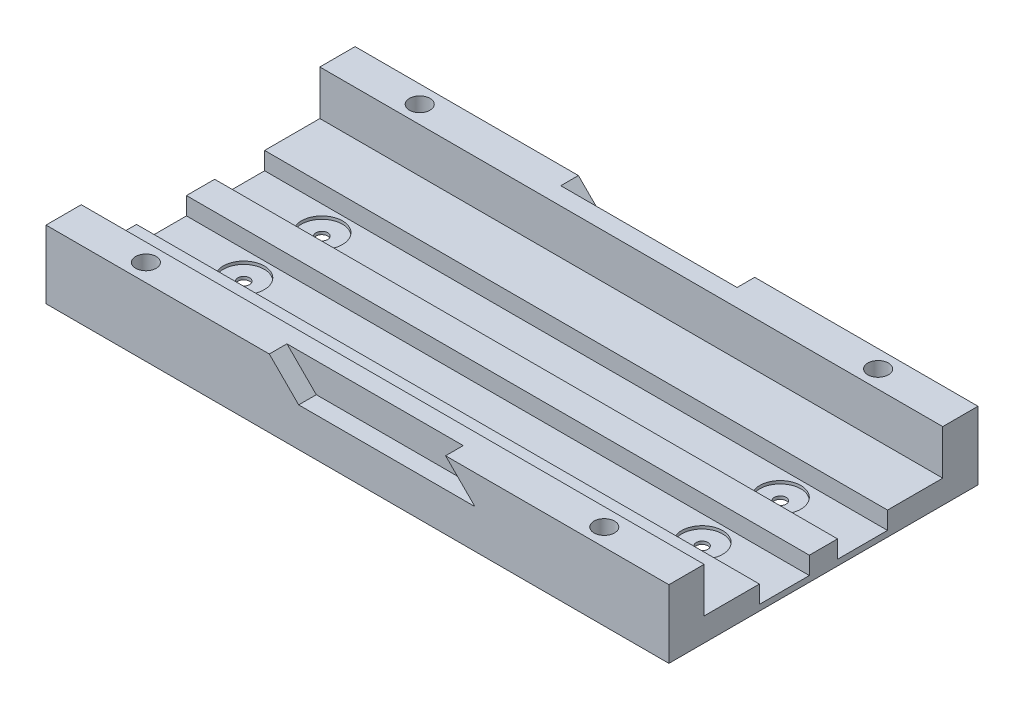
SolidWorks part; units mm, degrees
ref_plane "Front Plane" through (0, 0, 0) normal (0, 0, 1) x (1, 0, 0)
ref_plane "Top Plane" through (0, 0, 0) normal (0, 1, 0) x (1, 0, 0)
ref_plane "Right Plane" through (0, 0, 0) normal (1, 0, 0) x (0, 0, -1)
sketch "Sketch1" plane through (0, 0, 0) normal (0, 1, 0) x (1, 0, 0)
  line L1 (0, -13.3) -> (106, -13.3)
  line L2 (0, 0) -> (106, 0)
  line L3 (0, 0) -> (0, -4.8)
  line L4 (0, -4.8) -> (106, -4.8)
  line L5 (106, 0) -> (106, -4.8)
  line L6 (0, -13.3) -> (0, -4.8)
  line L7 (0, -4.8) -> (106, -4.8)
  line L8 (106, -13.3) -> (106, -4.8)
  line L9 (0, 0) -> (106, 0)
  line L10 (0, 0) -> (0, 8.5)
  line L11 (0, 8.5) -> (106, 8.5)
  line L12 (106, 0) -> (106, 8.5)
  line L13 (0, -22.7) -> (106, -22.7)
  line L14 (0, -22.7) -> (0, -13.3)
  line L15 (0, -13.3) -> (106, -13.3)
  line L16 (106, -22.7) -> (106, -13.3)
  line L17 (106, 8.5) -> (0, 8.5)
  line L18 (106, 8.5) -> (106, 17.9)
  line L19 (106, 17.9) -> (0, 17.9)
  line L20 (0, 8.5) -> (0, 17.9)
  line L21 (106, 17.9) -> (0, 17.9)
  line L22 (106, 17.9) -> (106, 23.9)
  line L23 (106, 23.9) -> (0, 23.9)
  line L24 (0, 17.9) -> (0, 23.9)
  line L25 (106, -28.7) -> (0, -28.7)
  line L26 (106, -28.7) -> (106, -22.7)
  line L27 (106, -22.7) -> (0, -22.7)
  line L28 (0, -28.7) -> (0, -22.7)
  dimension "D1" = 4.8
  dimension "D2" = 106
  dimension "D3" = 0
  dimension "D4" = 0
  dimension "D5" = 0
  dimension "D6" = 8.5
  dimension "D7" = 0
  dimension "D8" = 0
  dimension "D9" = 0
  dimension "D10" = 8.5
  dimension "D11" = 0
  dimension "D12" = 0
  dimension "D13" = 0
  dimension "D14" = 9.4
  dimension "D15" = 0
  dimension "D16" = 0
  dimension "D17" = 0
  dimension "D18" = 9.4
  dimension "D19" = 0
  dimension "D20" = 0
  dimension "D21" = 0
  dimension "D22" = 6
  dimension "D23" = 0
  dimension "D24" = 0
  dimension "D25" = 0
  dimension "D26" = 6
extrude "Boss-Extrude4" add sketch "Sketch1" along normal blind 4 contours L24 L19 L22 L23 | L20 L11 L18 L19 | L2 L12 L11 L10 | L5 L2 L3 L4 | L1 L8 L4 L6 | L13 L16 L1 L14 | L25 L28 L27 L26
sketch "Sketch4" plane through (0, 4, 0) normal (0, 1, 0) x (1, 0, 0)
  line L0 (106, -28.7) -> (106, 23.9) construction
  line L1 (0, -4.8) -> (106, -4.8)
  line L2 (0, -4.8) -> (0, 0)
  line L3 (0, 0) -> (106, 0)
  line L4 (106, -4.8) -> (106, 0)
  line L5 (0, -28.7) -> (0, 23.9) construction
  line L6 (106, 23.9) -> (0, 23.9) construction
  line L7 (106, -28.7) -> (0, -28.7) construction
  line L9 (106, 8.5) -> (0, 8.5)
  line L10 (106, 8.5) -> (106, 0)
  line L11 (106, 0) -> (0, 0)
  line L12 (0, 8.5) -> (0, 0)
  line L13 (106, -4.8) -> (0, -4.8)
  line L14 (106, -4.8) -> (106, -13.3)
  line L15 (106, -13.3) -> (0, -13.3)
  line L16 (0, -4.8) -> (0, -13.3)
  line M5 (0, 23.9) -> (0, -28.7)
  line M7 (106, -28.7) -> (106, 23.9)
  dimension "D1" = 0
  dimension "D2" = 23.9
  dimension "D3" = 23.9
  dimension "D4" = 0
  dimension "D5" = 8.5
  dimension "D6" = 8.5
extrude "Cut-Extrude2" cut sketch "Sketch4" against normal blind 3 contours L9 L3 M7 M5 | L15 L1 M7 M5
sketch "Sketch5" plane through (0, 4, 0) normal (0, 1, 0) x (1, 0, 0)
  line L0 (0, 8.5) -> (0, 23.9) construction
  line L1 (106, 23.9) -> (0, 23.9)
  line L2 (106, 23.9) -> (106, 17.9)
  line L3 (106, 17.9) -> (0, 17.9)
  line L4 (0, 23.9) -> (0, 17.9)
  line L5 (0, -28.7) -> (0, -13.3) construction
  line L6 (106, -28.7) -> (0, -28.7)
  line L7 (106, -28.7) -> (106, -22.7)
  line L8 (106, -22.7) -> (0, -22.7)
  line L9 (0, -28.7) -> (0, -22.7)
  dimension "D1" = 6
  dimension "D2" = 6
extrude "Boss-Extrude5" add sketch "Sketch5" along normal blind 7.6
sketch "Sketch6" plane through (0, 1, 0) normal (0, 1, 0) x (1, 0, 0)
  line L0 (0, -4.8) -> (106, -4.8) construction
  line L1 (106, -13.3) -> (106, -4.8) construction
  line L2 (0, -4.8) -> (0, -13.3) construction
  line L3 (106, -13.3) -> (0, -13.3) construction
  line L4 (106, 8.5) -> (0, 8.5) construction
  line L5 (106, 0) -> (106, 8.5) construction
  line L6 (0, 8.5) -> (0, 0) construction
  line L7 (0, 0) -> (106, 0) construction
  circle A0 centre (92, -9.05) radius 3.5
  circle A1 centre (14, -9.05) radius 3.5
  circle A2 centre (92, 4.25) radius 3.5
  circle A3 centre (14, 4.25) radius 3.5
  point P18 (106, 4.25)
  dimension "D1" = 7
  dimension "D5" = 7
  dimension "D7" = 7
  dimension "D10" = 7
  dimension "D2" = 4.25
  dimension "D3" = 14
  dimension "D4" = 14
  dimension "D6" = 4.25
  dimension "D8" = 4.25
  dimension "D9" = 14
  dimension "D11" = 14
  dimension "D12" = 4.25
extrude "Cut-Extrude3" cut sketch "Sketch6" against normal blind 0.5
sketch "Sketch7" plane through (0, 0.5, 0) normal (0, 1, 0) x (1, 0, 0)
  circle A0 centre (92, 4.25) radius 1
  circle A1 centre (92, -9.05) radius 1
  dimension "D1" = 2
  dimension "D2" = 2
sketch "Sketch8" plane through (0, 0.5, 0) normal (0, 1, 0) x (1, 0, 0)
  circle A0 centre (14, 4.25) radius 1
  circle A1 centre (14, -9.05) radius 1
  dimension "D1" = 2
  dimension "D2" = 2
extrude "Cut-Extrude4" cut sketch "Sketch8" against normal blind 20
extrude "Cut-Extrude5" cut sketch "Sketch7" against normal blind 20 contours A0
sketch "Sketch9" plane through (0, 0.5, 0) normal (0, 1, 0) x (1, 0, 0)
  circle A0 centre (92, -9.05) radius 1
  dimension "D1" = 2
extrude "Cut-Extrude6" cut sketch "Sketch9" against normal blind 20
sketch "Sketch10" plane through (0, 11.6, 0) normal (0, 1, 0) x (1, 0, 0)
  line L0 (106, 17.9) -> (106, 23.9) construction
  line L1 (106, 23.9) -> (0, 23.9) construction
  line L2 (0, 23.9) -> (0, 17.9) construction
  line L3 (106, -22.7) -> (0, -22.7) construction
  line L4 (106, -28.7) -> (106, -22.7) construction
  line L5 (0, -22.7) -> (0, -28.7) construction
  circle A0 centre (92, 20.9) radius 1.75
  circle A1 centre (14, 20.9) radius 1.75
  circle A2 centre (92, -25.7) radius 1.75
  circle A3 centre (14, -25.7) radius 1.75
  point P4 (106, 20.9)
  dimension "D3" = 3.5
  dimension "D4" = 3.5
  dimension "D7" = 3.5
  dimension "D10" = 3.5
  dimension "D1" = 14
  dimension "D2" = 3
  dimension "D5" = 14
  dimension "D6" = 3
  dimension "D8" = 3
  dimension "D9" = 14
  dimension "D11" = 14
  dimension "D12" = 3
extrude "Cut-Extrude7" cut sketch "Sketch10" against normal blind 20
sketch "Sketch11" plane through (0, 0, 0) normal (0, -1, 0) x (-1, 0, 0)
  circle A0 centre (-92, 20.9) radius 2.9
  circle A1 centre (-92, -25.7) radius 2.9
  circle A2 centre (-14, -25.7) radius 2.9
  circle A3 centre (-14, 20.9) radius 2.9
  dimension "D1" = 5.8
  dimension "D2" = 5.8
  dimension "D3" = 5.8
  dimension "D4" = 5.8
extrude "Cut-Extrude8" cut sketch "Sketch11" against normal blind 4.5
sketch "Sketch12" plane through (0, 0, -23.9) normal (0, 0, -1) x (-1, 0, 0)
  line L0 (-68, 11.6) -> (-73, 6.6)
  line L1 (-68, 11.6) -> (-38, 11.6)
  line L2 (-73, 6.6) -> (-43, 6.6)
  line L3 (-38, 11.6) -> (-43, 6.6)
  line L4 (-106, 11.6) -> (0, 11.6) construction
  line L6 (-106, 11.6) -> (-106, 0) construction
  dimension "D1" = 30
  dimension "D2" = 38
  dimension "D3" = 5
  dimension "D4" = 135
  dimension "D5" = 0
extrude "Cut-Extrude9" cut sketch "Sketch12" against normal blind 3
sketch "Sketch13" plane through (0, 0, 28.7) normal (0, 0, 1) x (1, 0, 0)
  line L0 (68, 11.6) -> (73, 6.6)
  line L1 (68, 11.6) -> (38, 11.6)
  line L2 (73, 6.6) -> (43, 6.6)
  line L3 (38, 11.6) -> (43, 6.6)
  line L4 (0, 11.6) -> (106, 11.6) construction
  dimension "D1" = 0
  dimension "D2" = 30
  dimension "D3" = 38
  dimension "D4" = 5
  dimension "D5" = 135
extrude "Cut-Extrude10" cut sketch "Sketch13" against normal blind 3
